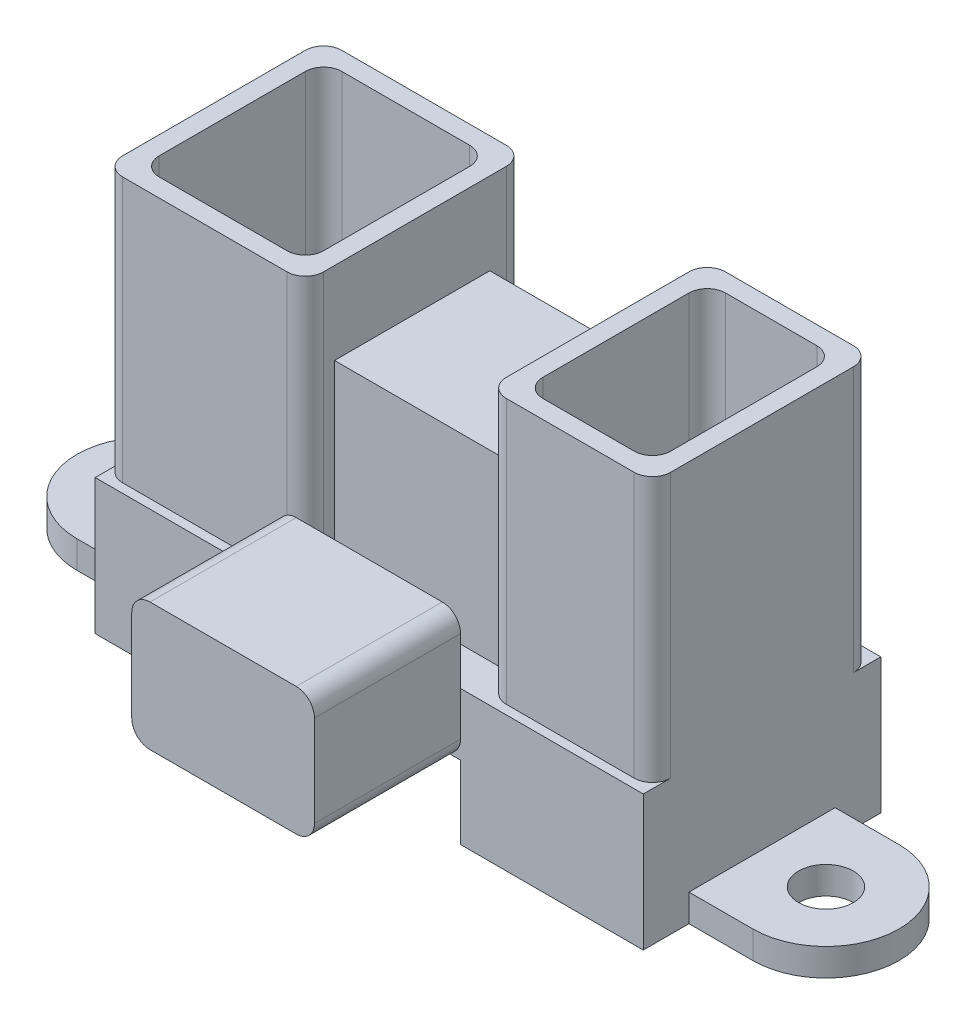
SolidWorks part; units mm, degrees
ref_plane "Front Plane" through (0, 0, 0) normal (0, 0, 1) x (1, 0, 0)
ref_plane "Top Plane" through (0, 0, 0) normal (0, 1, 0) x (1, 0, 0)
ref_plane "Right Plane" through (0, 0, 0) normal (1, 0, 0) x (0, 0, -1)
sketch "Sketch1" plane through (0, 0, 0) normal (0, 1, 0) x (1, 0, 0)
  line L1 (-15, 6.5) -> (15, 6.5)
  line L2 (-15, 6.5) -> (-15, -6.5)
  line L3 (-15, -6.5) -> (15, -6.5)
  line L4 (15, 6.5) -> (15, -6.5)
  line L5 (-15, 6.5) -> (15, -6.5) construction
  line L6 (-15, -6.5) -> (15, 6.5) construction
  point P0 (0, 0)
  dimension "D1" = 30
  dimension "D2" = 13
extrude "Boss-Extrude1" add sketch "Sketch1" along normal blind 7.4
sketch "Sketch2" plane through (0, 7.4, 0) normal (0, 1, 0) x (1, 0, 0)
  line L0 (-15, 6.5) -> (-15, -6.5) construction
  line L1 (-14, 6) -> (-5, 6)
  line L2 (-15, 5) -> (-15, -5)
  line L3 (-14, -6) -> (-5, -6)
  line L4 (-4, 5) -> (-4, -5)
  line L5 (-15, -6.5) -> (15, -6.5) construction
  line L6 (-13, 5) -> (-6, 5)
  line L7 (-14, 4) -> (-14, -4)
  line L8 (-13, -5) -> (-6, -5)
  line L9 (-5, 4) -> (-5, -4)
  line L10 (15, -6.5) -> (15, 6.5) construction
  line L11 (14, 6) -> (7, 6)
  line L12 (15, 5) -> (15, -5)
  line L13 (14, -6) -> (7, -6)
  line L14 (6, 5) -> (6, -5)
  line L16 (8, -5) -> (13, -5)
  line L17 (7, -4) -> (7, 4)
  line L18 (8, 5) -> (13, 5)
  line L19 (14, -4) -> (14, 4)
  arc A0 (13, -5) -> (14, -4) centre (13, -4) ccw
  arc A1 (7, 4) -> (8, 5) centre (8, 4) cw
  arc A2 (13, 5) -> (14, 4) centre (13, 4) cw
  arc A3 (8, -5) -> (7, -4) centre (8, -4) cw
  arc A4 (7, 6) -> (6, 5) centre (7, 5) ccw
  arc A5 (15, -5) -> (14, -6) centre (14, -5) cw
  arc A6 (7, -6) -> (6, -5) centre (7, -5) cw
  arc A7 (14, 6) -> (15, 5) centre (14, 5) cw
  arc A8 (-6, 5) -> (-5, 4) centre (-6, 4) cw
  arc A9 (-14, -4) -> (-13, -5) centre (-13, -4) ccw
  arc A10 (-6, -5) -> (-5, -4) centre (-6, -4) ccw
  arc A11 (-13, 5) -> (-14, 4) centre (-13, 4) ccw
  arc A12 (-5, 6) -> (-4, 5) centre (-5, 5) cw
  arc A13 (-15, -5) -> (-14, -6) centre (-14, -5) ccw
  arc A14 (-5, -6) -> (-4, -5) centre (-5, -5) ccw
  arc A15 (-14, 6) -> (-15, 5) centre (-14, 5) ccw
  point P34 (15, -6)
  point P37 (6, -6)
  point P40 (15, 6)
  point P53 (-15, -6)
  point P56 (-4, -6)
  point P59 (-15, 6)
  dimension "D14" = 1
  dimension "D1" = 12
  dimension "D2" = 0.5
  dimension "D3" = 1
  dimension "D4" = 1
  dimension "D5" = 1
  dimension "D6" = 1
  dimension "D7" = 11
  dimension "D8" = 12
  dimension "D9" = 9
  dimension "D10" = 1
  dimension "D11" = 1
  dimension "D12" = 1
  dimension "D13" = 1
extrude "Boss-Extrude2" add sketch "Sketch2" along normal blind 14.5
sketch "Sketch3" plane through (0, 7.4, 0) normal (0, 1, 0) x (1, 0, 0)
  line L0 (-4, -5) -> (-4, 5) construction
  line L1 (-4, 4.1) -> (6, 4.1)
  line L2 (-4, 4.1) -> (-4, -4.4)
  line L3 (-4, -4.4) -> (6, -4.4)
  line L4 (6, 4.1) -> (6, -4.4)
  line L5 (6, 5) -> (6, -5) construction
  line L6 (15, 6.5) -> (-15, 6.5) construction
  dimension "D1" = 2.4
  dimension "D2" = 8.5
extrude "Boss-Extrude3" add sketch "Sketch3" along normal blind 10
sketch "Sketch5" plane through (0, 0, 0) normal (0, 1, 0) x (1, 0, 0)
  line L0 (-18.5, 0) -> (18.5, 0) construction
  line L1 (-18.5, 4) -> (18.5, 4)
  line L2 (-18.5, -4) -> (18.5, -4)
  arc A0 (-18.5, 4) -> (-18.5, -4) centre (-18.5, 0) ccw
  arc A1 (18.5, -4) -> (18.5, 4) centre (18.5, 0) ccw
  circle A2 centre (-18.5, 0) radius 1.5
  circle A3 centre (18.5, 0) radius 1.5
  point P3 (0, 0)
  dimension "D2" = 4
  dimension "D3" = 3
  dimension "D4" = 3
  dimension "D1" = 37
extrude "Boss-Extrude4" add sketch "Sketch5" along normal blind 1.5
sketch "Sketch6" plane through (0, 0, 0) normal (0, -1, 0) x (1, 0, 0)
  line L0 (-15, 4) -> (-15, 6.5) construction
  line L1 (-14, 5.5) -> (-5, 5.5)
  line L2 (-14, 5.5) -> (-14, -5.5)
  line L3 (-14, -5.5) -> (14, -5.5)
  line L4 (14, 5.5) -> (14, -5.5)
  line L5 (-15, 6.5) -> (15, 6.5) construction
  line L6 (15, -6.5) -> (-15, -6.5) construction
  line L7 (15, -4) -> (15, -6.5) construction
  line L8 (-5, 5.5) -> (-5, 6.5)
  line L9 (-5, 6.5) -> (5, 6.5)
  line L10 (5, 6.5) -> (5, 5.5)
  line L11 (5, 5.5) -> (14, 5.5)
  point P6 (-15, 5.25)
  dimension "D1" = 1
  dimension "D2" = 1
  dimension "D3" = 1
  dimension "D4" = 1
  dimension "D5" = 9
  dimension "D6" = 9
extrude "Cut-Extrude2" cut sketch "Sketch6" against normal blind 4
sketch "Sketch7" plane through (0, 0, 6.5) normal (0, 0, 1) x (1, 0, 0)
  line L0 (5, 4) -> (-5, 4) construction
  line L1 (-5, 4) -> (5, 4)
  line L2 (-5, 4) -> (-5, 11)
  line L3 (-5, 11) -> (5, 11)
  line L4 (5, 4) -> (5, 11)
  line L5 (0, 0) -> (0, 4) construction
  dimension "D1" = 10
  dimension "D2" = 7
extrude "Boss-Extrude5" add sketch "Sketch7" along normal blind 8
fillet "Fillet1" radius 1 4 edges at (-5, 11, 10.5) (-5, 4, 10.5) (5, 11, 10.5) (5, 4, 10.5)
